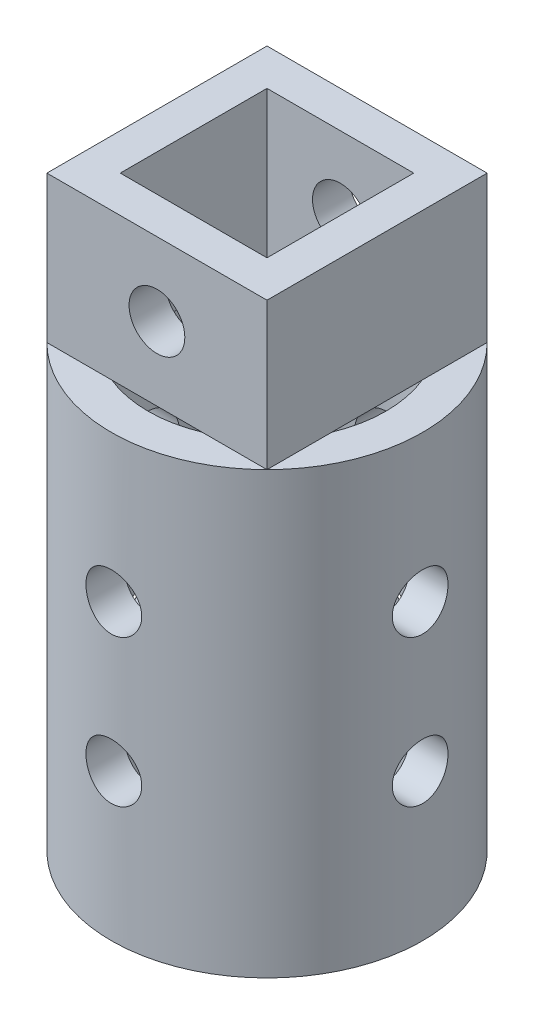
SolidWorks part; units mm, degrees
ref_plane "Front Plane" through (0, 0, 0) normal (0, 0, 1) x (1, 0, 0)
ref_plane "Top Plane" through (0, 0, 0) normal (0, 1, 0) x (1, 0, 0)
ref_plane "Right Plane" through (0, 0, 0) normal (1, 0, 0) x (0, 0, -1)
sketch "Sketch2" plane through (0, 0, 0) normal (0, 1, 0) x (1, 0, 0)
  line L1 (-19.05, -19.05) -> (19.05, -19.05)
  line L2 (-19.05, -19.05) -> (-19.05, 19.05)
  line L3 (-19.05, 19.05) -> (19.05, 19.05)
  line L4 (19.05, -19.05) -> (19.05, 19.05)
  line L5 (-19.05, -19.05) -> (19.05, 19.05) construction
  line L6 (-19.05, 19.05) -> (19.05, -19.05) construction
  line L7 (12.7, -12.7) -> (-12.7, -12.7)
  line L8 (12.7, -12.7) -> (12.7, 12.7)
  line L9 (12.7, 12.7) -> (-12.7, 12.7)
  line L10 (-12.7, -12.7) -> (-12.7, 12.7)
  line L11 (12.7, -12.7) -> (-12.7, 12.7) construction
  line L12 (12.7, 12.7) -> (-12.7, -12.7) construction
  circle A0 centre (0, 0) radius 27.3609
  dimension "D1" = 38.1
  dimension "D2" = 38.1
  dimension "D3" = 25.4
  dimension "D4" = 25.4
extrude "Boss-Extrude1" add sketch "Sketch2" along normal blind 25.4 contours L1 L4 L3 L2 L7 L10 L9 L8
sketch "Sketch3" plane through (0, 0, 0) normal (0, -1, 0) x (1, 0, 0)
  circle A0 centre (0, 0) radius 26.9408
  circle A1 centre (0, 0) radius 20.5908
  dimension "D1" = 6.35
extrude "Boss-Extrude2" add sketch "Sketch3" along normal blind 76.2
sketch "Sketch4" plane through (0, 0, 19.05) normal (0, 0, 1) x (1, 0, 0)
  line L0 (-19.05, 25.4) -> (-19.05, 0) construction
  line L1 (-7.8152, 0) -> (7.8152, 0) construction
  circle A0 centre (0, 12.7) radius 4.826
  dimension "D3" = 9.652
  dimension "D1" = 19.05
  dimension "D2" = 12.7
extrude "Cut-Extrude1" cut sketch "Sketch4" against normal blind 50.8
sketch "Sketch5" plane through (0, 0, 0) normal (0, 0, 1) x (1, 0, 0)
  line L0 (-26.9408, -76.2) -> (26.9408, -76.2) construction
  circle A0 centre (0, -25.4) radius 4.826
  circle A1 centre (0, -50.8) radius 4.826
  point P6 (0, 0)
  point P7 (0, 0)
  dimension "D1" = 9.652
  dimension "D2" = 9.652
  dimension "D3" = 25.4
  dimension "D4" = 25.4
extrude "Cut-Extrude2" cut sketch "Sketch5" against normal through all both and the other way through all contours A0 | A1
sketch "Sketch6" plane through (0, 0, 0) normal (1, 0, 0) x (0, 0, -1)
  line L0 (-26.9408, -76.2) -> (26.9408, -76.2) construction
  circle A0 centre (0, -50.8) radius 4.826
  circle A1 centre (0, -25.4) radius 4.826
  point P6 (0, 0)
  dimension "D1" = 9.652
  dimension "D2" = 9.652
  dimension "D3" = 25.4
  dimension "D4" = 25.4
extrude "Cut-Extrude3" cut sketch "Sketch6" against normal through all both and the other way through all
